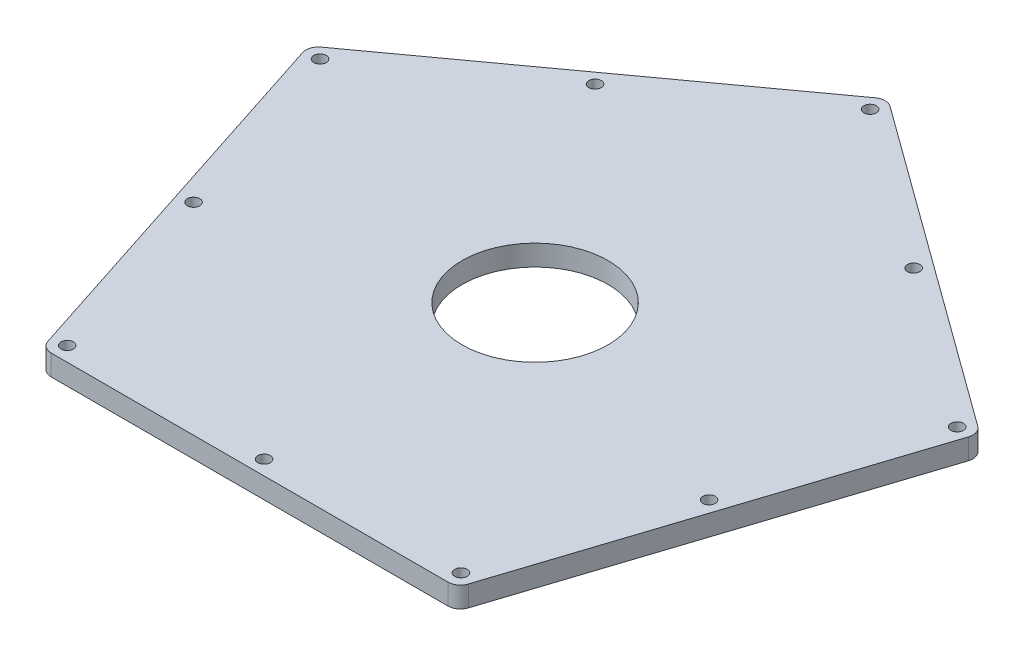
SolidWorks part; units mm, degrees
material "PVC Rigid"
ref_plane "Front Plane" through (0, 0, 0) normal (0, 0, 1) x (1, 0, 0)
ref_plane "Top Plane" through (0, 0, 0) normal (0, 1, 0) x (1, 0, 0)
ref_plane "Right Plane" through (0, 0, 0) normal (1, 0, 0) x (0, 0, -1)
ref_plane "Plane1" through (0, -10, 0) normal (0, 1, 0) x (1, 0, 0)
sketch "Sketch7" plane through (0, -10, 0) normal (0, 1, 0) x (1, 0, 0)
  line L1 (80.9017, 26.2866) -> (0, 85.0651)
  line L3 (50, -68.8191) -> (80.9017, 26.2866)
  line L5 (-50, -68.8191) -> (50, -68.8191)
  line L8 (0, 85.0651) -> (-80.9017, 26.2866)
  line L9 (-80.9017, 26.2866) -> (-50, -68.8191)
  circle A10 centre (62.1222, -20.1847) radius 1.5
  circle A11 centre (47.4571, -65.3191) radius 1.5
  circle A12 centre (0, -65.3191) radius 1.5
  circle A13 centre (-47.4571, -65.3191) radius 1.5
  circle A14 centre (-62.1222, -20.1847) radius 1.5
  circle A15 centre (-76.7872, 24.9497) radius 1.5
  circle A16 centre (-38.3936, 52.8443) radius 1.5
  circle A17 centre (0, 80.7388) radius 1.5
  circle A18 centre (76.7872, 24.9497) radius 1.5
  circle A19 centre (38.3936, 52.8443) radius 1.5
extrude "Boss-Extrude1" add sketch "Sketch7" along normal blind 5
sketch "Sketch8" plane through (0, -5, 0) normal (0, 1, 0) x (1, 0, 0)
  circle A0 centre (0, 0) radius 17.6
  dimension "D1" = 35.2
extrude "Cut-Extrude1" cut sketch "Sketch8" against normal blind 5
fillet "Fillet1" radius 3 5 edges at (-50, -7.5, 68.8191) (-80.9017, -7.5, -26.2866) (0, -7.5, -85.0651) (50, -7.5, 68.8191) (80.9017, -7.5, -26.2866)
